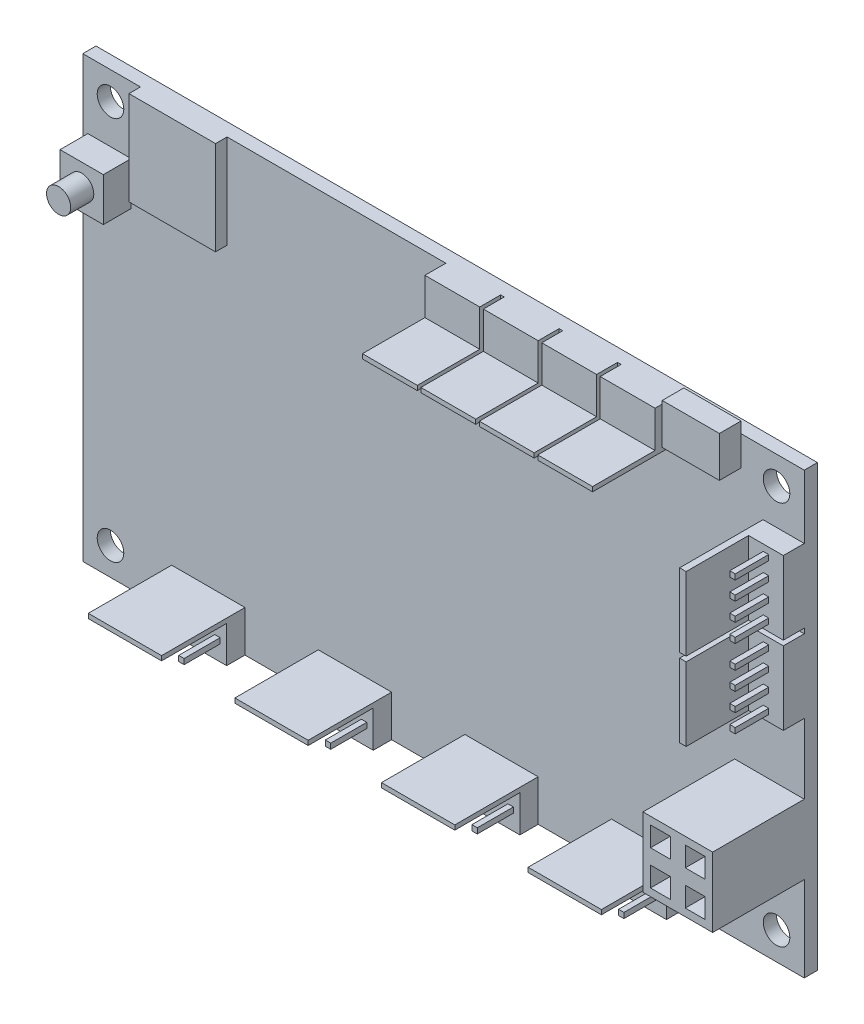
SolidWorks part; units mm, degrees
ref_plane "Front Plane" through (0, 0, 0) normal (0, 0, 1) x (1, 0, 0)
ref_plane "Top Plane" through (0, 0, 0) normal (0, 1, 0) x (1, 0, 0)
ref_plane "Right Plane" through (0, 0, 0) normal (1, 0, 0) x (0, 0, -1)
sketch "Sketch1" plane through (0, 0, 0) normal (0, 0, 1) x (1, 0, 0)
  line L1 (0, 0) -> (100, 0)
  line L2 (0, 0) -> (0, 60.96)
  line L3 (0, 60.96) -> (100, 60.96)
  line L4 (100, 0) -> (100, 60.96)
  dimension "D1" = 60.96
  dimension "D2" = 100
extrude "Boss-Extrude1" add sketch "Sketch1" along normal blind 1.8288
sketch "Sketch2" plane through (0, 0, 1.8288) normal (0, 0, 1) x (1, 0, 0)
  line L0 (0, 0) -> (100, 0) construction
  line L1 (12.319, 5.715) -> (22.479, 5.715)
  line L2 (12.319, 5.715) -> (12.319, 0)
  line L3 (12.319, 0) -> (22.479, 0)
  line L4 (22.479, 5.715) -> (22.479, 0)
  line L5 (12.319, 5.715) -> (22.479, 0) construction
  line L6 (12.319, 0) -> (22.479, 5.715) construction
  line L7 (0, 60.96) -> (0, 0) construction
  line L8 (32.639, 5.715) -> (42.799, 0) construction
  line L9 (32.639, 0) -> (42.799, 5.715) construction
  line L10 (32.639, 5.715) -> (42.799, 5.715)
  line L11 (42.799, 5.715) -> (42.799, 0)
  line L12 (32.639, 0) -> (42.799, 0)
  line L13 (32.639, 5.715) -> (32.639, 0)
  line L14 (52.959, 5.715) -> (63.119, 0) construction
  line L15 (52.959, 0) -> (63.119, 5.715) construction
  line L16 (52.959, 5.715) -> (63.119, 5.715)
  line L17 (63.119, 5.715) -> (63.119, 0)
  line L18 (52.959, 0) -> (63.119, 0)
  line L19 (52.959, 5.715) -> (52.959, 0)
  line L20 (73.279, 5.715) -> (83.439, 0) construction
  line L21 (73.279, 0) -> (83.439, 5.715) construction
  line L22 (73.279, 5.715) -> (83.439, 5.715)
  line L23 (83.439, 5.715) -> (83.439, 0)
  line L24 (73.279, 0) -> (83.439, 0)
  line L25 (73.279, 5.715) -> (73.279, 0)
  line L26 (12.319, 5.715) -> (32.639, 5.715) construction
  line L27 (100, 0) -> (100, 60.96) construction
  line L28 (100, 52.16) -> (94.285, 52.16)
  line L29 (100, 52.16) -> (100, 42)
  line L30 (100, 42) -> (94.285, 42)
  line L31 (94.285, 52.16) -> (94.285, 42)
  line L32 (100, 52.16) -> (94.285, 42) construction
  line L33 (100, 42) -> (94.285, 52.16) construction
  line L34 (100, 60.96) -> (0, 60.96) construction
  line L35 (100, 41.32) -> (94.285, 41.32)
  line L36 (100, 41.32) -> (100, 31.16)
  line L37 (100, 31.16) -> (94.285, 31.16)
  line L38 (94.285, 41.32) -> (94.285, 31.16)
  line L39 (100, 41.32) -> (94.285, 31.16) construction
  line L40 (100, 31.16) -> (94.285, 41.32) construction
  point P4 (17.399, 2.8575)
  point P27 (97.1425, 47.08)
  point P34 (97.1425, 36.24)
  dimension "D1" = 10.16
  dimension "D2" = 5.715
  dimension "D3" = 12.319
  dimension "D5" = 20.32
  dimension "D6" = 21
  dimension "D7" = 8.8
  dimension "D4" = 4
extrude "4 pin molex" add sketch "Sketch2" along normal blind 11.557
sketch "Sketch3" plane through (83.439, 0, 0) normal (1, 0, 0) x (0, 0, -1)
  line L0 (-13.3858, 5.715) -> (-1.8288, 5.715) construction
  line L1 (-13.3858, 0) -> (-4.3688, 0)
  line L2 (-13.3858, 0) -> (-13.3858, 5.08)
  line L3 (-13.3858, 5.08) -> (-4.3688, 5.08)
  line L4 (-4.3688, 0) -> (-4.3688, 5.08)
  line L5 (-13.3858, 0) -> (-4.3688, 5.08) construction
  line L6 (-13.3858, 5.08) -> (-4.3688, 0) construction
  line L7 (-1.8288, 0) -> (-1.8288, 31.16) construction
  point P4 (-8.8773, 2.54)
  dimension "D1" = 0.635
  dimension "D2" = 2.54
extrude "Cut-Extrude1" cut sketch "Sketch3" against normal through all
sketch "Sketch7" plane through (0, 31.16, 0) normal (0, -1, 0) x (-1, 0, 0)
  line L1 (-100, -13.3858) -> (-95.185, -13.3858)
  line L2 (-100, -13.3858) -> (-100, -4.7288)
  line L3 (-100, -4.7288) -> (-95.185, -4.7288)
  line L4 (-95.185, -13.3858) -> (-95.185, -4.7288)
  line L5 (-100, -13.3858) -> (-95.185, -4.7288) construction
  line L6 (-100, -4.7288) -> (-95.185, -13.3858) construction
  line L8 (-94.285, -13.3858) -> (-94.285, -1.8288) construction
  line L9 (-83.439, -1.8288) -> (-100, -1.8288) construction
  point P4 (-97.5925, -9.0573)
  dimension "D1" = 0.9
  dimension "D2" = 2.9
extrude "Cut-Extrude2" cut sketch "Sketch7" against normal blind 24.6
sketch "Sketch4" plane through (0, 0, 1.8288) normal (0, 0, 1) x (1, 0, 0)
  line L0 (100, 0) -> (100, 31.16) construction
  line L1 (100, 21.463) -> (90.348, 21.463)
  line L2 (100, 21.463) -> (100, 11.811)
  line L3 (100, 11.811) -> (90.348, 11.811)
  line L4 (90.348, 21.463) -> (90.348, 11.811)
  line L5 (100, 21.463) -> (90.348, 11.811) construction
  line L6 (100, 11.811) -> (90.348, 21.463) construction
  line L7 (83.439, 0) -> (100, 0) construction
  point P4 (95.174, 16.637)
  dimension "D1" = 9.652
  dimension "D2" = 9.652
  dimension "D3" = 11.811
extrude "Power Connector" add sketch "Sketch4" along normal blind 12.7
sketch "Sketch5" plane through (0, 0, 1.8288) normal (0, 0, 1) x (1, 0, 0)
  line L0 (100, 21.463) -> (100, 31.16) construction
  line L1 (83.3122, 56.8452) -> (91.237, 56.8452)
  line L2 (83.3122, 56.8452) -> (83.3122, 62.484)
  line L3 (83.3122, 62.484) -> (91.237, 62.484)
  line L4 (91.237, 56.8452) -> (91.237, 62.484)
  line L5 (83.3122, 56.8452) -> (91.237, 62.484) construction
  line L6 (83.3122, 62.484) -> (91.237, 56.8452) construction
  line L7 (100, 60.96) -> (0, 60.96) construction
  point P4 (87.2746, 59.6646)
  dimension "D1" = 7.9248
  dimension "D2" = 5.6388
  dimension "D3" = 8.763
  dimension "D4" = 1.524
extrude "MicroUSB" add sketch "Sketch5" along normal blind 3
sketch "Sketch6" plane through (0, 0, 1.8288) normal (0, 0, 1) x (1, 0, 0)
  line L0 (83.3122, 60.96) -> (0, 60.96) construction
  line L1 (8, 60.96) -> (20, 60.96)
  line L2 (8, 60.96) -> (8, 47.96)
  line L3 (8, 47.96) -> (20, 47.96)
  line L4 (20, 60.96) -> (20, 47.96)
  line L5 (8, 60.96) -> (20, 47.96) construction
  line L6 (8, 47.96) -> (20, 60.96) construction
  line L7 (0, 60.96) -> (0, 0) construction
  point P4 (14, 54.46)
  dimension "D1" = 12
  dimension "D2" = 13
  dimension "D3" = 8
extrude "MicroSD" add sketch "Sketch6" along normal blind 1.6
sketch "Sketch8" plane through (0, 0, 1.8288) normal (0, 0, 1) x (1, 0, 0)
  line L0 (0, 60.96) -> (0, 0) construction
  line L1 (0.7, 51.71) -> (6.7, 51.71)
  line L2 (0.7, 51.71) -> (0.7, 45.71)
  line L3 (0.7, 45.71) -> (6.7, 45.71)
  line L4 (6.7, 51.71) -> (6.7, 45.71)
  line L5 (0.7, 51.71) -> (6.7, 45.71) construction
  line L6 (0.7, 45.71) -> (6.7, 51.71) construction
  line L7 (8, 60.96) -> (0, 60.96) construction
  point P4 (3.7, 48.71)
  dimension "D1" = 6
  dimension "D2" = 6
  dimension "D3" = 6.7
  dimension "D4" = 9.25
extrude "Boss-Extrude6" add sketch "Sketch8" along normal blind 3.85
sketch "Sketch9" plane through (0, 0, 5.6788) normal (0, 0, 1) x (1, 0, 0)
  line L0 (0.7, 48.71) -> (3.7, 48.71) construction
  line L1 (0.7, 51.71) -> (0.7, 45.71) construction
  line L2 (3.7, 48.71) -> (3.7, 51.71) construction
  line L3 (6.7, 51.71) -> (0.7, 51.71) construction
  circle A0 centre (3.7, 48.71) radius 1.675
  dimension "D1" = 3.35
extrude "Boss-Extrude7" add sketch "Sketch9" along normal blind 3.2
sketch "Sketch10" plane through (0, 0, 1.8288) normal (0, 0, 1) x (1, 0, 0)
  line L0 (83.3122, 60.96) -> (20, 60.96) construction
  line L1 (82.22, 60.96) -> (74.62, 60.96)
  line L2 (82.22, 60.96) -> (82.22, 55.245)
  line L3 (82.22, 55.245) -> (74.62, 55.245)
  line L4 (74.62, 60.96) -> (74.62, 55.245)
  line L5 (82.22, 60.96) -> (74.62, 55.245) construction
  line L6 (82.22, 55.245) -> (74.62, 60.96) construction
  line L7 (100, 52.16) -> (100, 60.96) construction
  line L8 (74.12, 55.245) -> (66.52, 55.245)
  line L9 (66.52, 60.96) -> (66.52, 55.245)
  line L10 (74.12, 55.245) -> (66.52, 60.96) construction
  line L11 (74.12, 60.96) -> (66.52, 55.245) construction
  line L12 (74.12, 60.96) -> (66.52, 60.96)
  line L13 (74.12, 60.96) -> (74.12, 55.245)
  line L14 (66.02, 55.245) -> (58.42, 55.245)
  line L15 (58.42, 60.96) -> (58.42, 55.245)
  line L16 (66.02, 55.245) -> (58.42, 60.96) construction
  line L17 (66.02, 60.96) -> (58.42, 55.245) construction
  line L18 (66.02, 60.96) -> (58.42, 60.96)
  line L19 (66.02, 60.96) -> (66.02, 55.245)
  line L20 (57.92, 55.245) -> (50.32, 55.245)
  line L21 (50.32, 60.96) -> (50.32, 55.245)
  line L22 (57.92, 55.245) -> (50.32, 60.96) construction
  line L23 (57.92, 60.96) -> (50.32, 55.245) construction
  line L24 (57.92, 60.96) -> (50.32, 60.96)
  line L25 (57.92, 60.96) -> (57.92, 55.245)
  line L26 (82.22, 55.245) -> (74.12, 55.245) construction
  point P4 (78.42, 58.1025)
  dimension "D1" = 7.6
  dimension "D2" = 5.715
  dimension "D3" = 17.78
  dimension "D5" = 8.1
  dimension "D4" = 4
extrude "Boss-Extrude8" add sketch "Sketch10" along normal blind 11.557
sketch "Sketch11" plane through (82.22, 0, 0) normal (1, 0, 0) x (0, 0, -1)
  line L0 (-13.3858, 55.245) -> (-1.8288, 55.245) construction
  line L1 (-13.3858, 60.96) -> (-4.7288, 60.96)
  line L2 (-13.3858, 60.96) -> (-13.3858, 55.88)
  line L3 (-13.3858, 55.88) -> (-4.7288, 55.88)
  line L4 (-4.7288, 60.96) -> (-4.7288, 55.88)
  line L5 (-13.3858, 60.96) -> (-4.7288, 55.88) construction
  line L6 (-13.3858, 55.88) -> (-4.7288, 60.96) construction
  line L7 (-1.8288, 52.16) -> (-1.8288, 60.96) construction
  point P4 (-9.0573, 58.42)
  dimension "D1" = 0.635
  dimension "D2" = 2.9
extrude "Cut-Extrude3" cut sketch "Sketch11" against normal blind 36.449
sketch "Sketch13" plane through (0, 0, 1.8288) normal (0, 0, 1) x (1, 0, 0)
  line L0 (8, 60.96) -> (0, 60.96) construction
  line L1 (0, 60.96) -> (0, 0) construction
  line L2 (100, 0) -> (100, 11.811) construction
  line L3 (83.439, 0) -> (100, 0) construction
  circle A0 centre (3.8415, 57.1185) radius 1.8415
  circle A1 centre (3.8415, 3.8415) radius 1.8415
  circle A2 centre (96.1585, 3.8415) radius 1.8415
  circle A3 centre (96.1585, 57.1185) radius 1.8415
  dimension "D1" = 3.683
  dimension "D2" = 2
  dimension "D3" = 2
  dimension "D4" = 2
  dimension "D5" = 2
extrude "Cut-Extrude4" cut sketch "Sketch13" against normal blind 36.449
sketch "Sketch14" plane through (0, 0, 14.5288) normal (0, 0, 1) x (1, 0, 0)
  line L0 (96.212, 20.425) -> (98.962, 17.675) construction
  line L1 (90.348, 21.463) -> (100, 21.463)
  line L2 (90.348, 21.463) -> (90.348, 11.811)
  line L3 (90.348, 11.811) -> (100, 11.811)
  line L4 (100, 21.463) -> (100, 11.811)
  line L5 (95.174, 11.811) -> (95.174, 21.463) construction
  line L6 (90.348, 16.637) -> (100, 16.637) construction
  line L7 (92.761, 14.224) -> (97.587, 14.224) construction
  line L8 (92.761, 14.224) -> (92.761, 19.05) construction
  line L9 (92.761, 19.05) -> (97.587, 19.05) construction
  line L10 (97.587, 14.224) -> (97.587, 19.05) construction
  line L11 (92.761, 14.224) -> (97.587, 19.05) construction
  line L12 (92.761, 19.05) -> (97.587, 14.224) construction
  line L13 (91.386, 17.675) -> (94.136, 17.675)
  line L14 (91.386, 17.675) -> (91.386, 20.425)
  line L15 (91.386, 20.425) -> (94.136, 20.425)
  line L16 (94.136, 17.675) -> (94.136, 20.425)
  line L17 (91.386, 17.675) -> (94.136, 20.425) construction
  line L18 (91.386, 20.425) -> (94.136, 17.675) construction
  line L19 (96.212, 17.675) -> (98.962, 20.425) construction
  line L20 (96.212, 17.675) -> (98.962, 17.675)
  line L21 (96.212, 17.675) -> (96.212, 20.425)
  line L22 (96.212, 20.425) -> (98.962, 20.425)
  line L23 (98.962, 17.675) -> (98.962, 20.425)
  line L24 (96.212, 15.599) -> (98.962, 12.849) construction
  line L25 (96.212, 12.849) -> (98.962, 15.599) construction
  line L26 (96.212, 12.849) -> (98.962, 12.849)
  line L27 (96.212, 12.849) -> (96.212, 15.599)
  line L28 (96.212, 15.599) -> (98.962, 15.599)
  line L29 (98.962, 12.849) -> (98.962, 15.599)
  line L30 (91.386, 15.599) -> (94.136, 12.849) construction
  line L31 (91.386, 12.849) -> (94.136, 15.599) construction
  line L32 (91.386, 12.849) -> (94.136, 12.849)
  line L33 (91.386, 12.849) -> (91.386, 15.599)
  line L34 (91.386, 15.599) -> (94.136, 15.599)
  line L35 (94.136, 12.849) -> (94.136, 15.599)
  line L36 (91.386, 20.425) -> (96.212, 20.425) construction
  line L37 (91.386, 20.425) -> (91.386, 15.599) construction
  point P4 (95.174, 16.637)
  point P56 (95.174, 16.637)
  dimension "D1" = 4.826
  dimension "D2" = 2.75
  dimension "D5" = 90
  dimension "D6" = 4.826
  dimension "D7" = 4.826
  dimension "D3" = 2
  dimension "D4" = 2
extrude "Cut-Extrude5" cut sketch "Sketch14" against normal blind 5 contours L26 L29 L28 L27 | L32 L35 L34 L33 | L13 L16 L15 L14 | L20 L23 L22 L21
sketch "Sketch15" plane through (0, 0, 4.3688) normal (0, 0, 1) x (1, 0, 0)
  line L0 (52.959, 0) -> (52.959, 5.08) construction
  line L1 (22.479, 0) -> (12.319, 0)
  line L2 (22.479, 0) -> (22.479, 5.08)
  line L3 (22.479, 5.08) -> (12.319, 5.08)
  line L4 (12.319, 0) -> (12.319, 5.08)
  line L5 (17.399, 5.08) -> (17.399, 0) construction
  line L6 (22.479, 2.54) -> (12.319, 2.54) construction
  line L7 (42.799, 0) -> (32.639, 0)
  line L8 (42.799, 0) -> (42.799, 5.08)
  line L9 (42.799, 5.08) -> (32.639, 5.08)
  line L10 (32.639, 0) -> (32.639, 5.08)
  line L11 (37.719, 5.08) -> (37.719, 0) construction
  line L12 (42.799, 2.54) -> (32.639, 2.54) construction
  line L13 (63.119, 0) -> (52.959, 0)
  line L14 (63.119, 0) -> (63.119, 5.08)
  line L15 (63.119, 5.08) -> (52.959, 5.08)
  line L16 (52.959, 0) -> (52.959, 5.08)
  line L17 (58.039, 5.08) -> (58.039, 0) construction
  line L18 (63.119, 2.54) -> (52.959, 2.54) construction
  line L19 (52.959, 5.715) -> (52.959, 0) construction
  line L20 (94.285, 31.16) -> (100, 31.16) construction
  line L21 (83.439, 0) -> (73.279, 0)
  line L22 (83.439, 0) -> (83.439, 5.08)
  line L23 (83.439, 5.08) -> (73.279, 5.08)
  line L24 (73.279, 0) -> (73.279, 5.08)
  line L25 (78.359, 5.08) -> (78.359, 0) construction
  line L26 (83.439, 2.54) -> (73.279, 2.54) construction
  line L27 (100, 41.32) -> (95.185, 41.32)
  line L28 (100, 41.32) -> (100, 31.16)
  line L29 (100, 31.16) -> (95.185, 31.16)
  line L30 (95.185, 41.32) -> (95.185, 31.16)
  line L31 (97.5925, 31.16) -> (97.5925, 41.32) construction
  line L32 (100, 36.24) -> (95.185, 36.24) construction
  line L33 (94.285, 31.16) -> (95.185, 31.16) construction
  line L34 (100, 41.32) -> (94.285, 41.32) construction
  line L35 (95.185, 42) -> (100, 42)
  line L36 (95.185, 42) -> (95.185, 52.16)
  line L37 (95.185, 52.16) -> (100, 52.16)
  line L38 (100, 42) -> (100, 52.16)
  line L39 (97.5925, 52.16) -> (97.5925, 42) construction
  line L40 (95.185, 47.08) -> (100, 47.08) construction
  point P9 (54.229, 2.54)
  point P56 (56.769, 2.54)
  point P61 (59.309, 2.54)
  point P66 (61.849, 2.54)
  point P88 (37.719, 2.54)
  point P93 (58.039, 2.54)
  point P104 (54.229, 2.54)
  point P105 (78.359, 2.54)
  point P183 (97.5925, 47.08)
  point P207 (97.5925, 36.24)
  line B0 (57.144, 2.165) -> (56.394, 2.165)
  line B1 (54.604, 2.165) -> (53.854, 2.165)
  line B2 (54.604, 2.165) -> (54.604, 2.915)
  line B3 (54.604, 2.915) -> (53.854, 2.915)
  line B4 (53.854, 2.165) -> (53.854, 2.915)
  line B5 (57.144, 2.165) -> (57.144, 2.915)
  line B6 (57.144, 2.915) -> (56.394, 2.915)
  line B7 (56.394, 2.165) -> (56.394, 2.915)
  line B8 (59.684, 2.165) -> (58.934, 2.165)
  line B9 (59.684, 2.165) -> (59.684, 2.915)
  line B10 (59.684, 2.915) -> (58.934, 2.915)
  line B11 (58.934, 2.165) -> (58.934, 2.915)
  line B12 (62.224, 2.165) -> (61.474, 2.165)
  line B13 (62.224, 2.165) -> (62.224, 2.915)
  line B14 (62.224, 2.915) -> (61.474, 2.915)
  line B15 (61.474, 2.165) -> (61.474, 2.915)
  line B16 (54.604, 2.165) -> (53.854, 2.915) construction
  line B17 (54.604, 2.915) -> (53.854, 2.165) construction
  line B18 (57.144, 2.165) -> (56.394, 2.915) construction
  line B19 (57.144, 2.915) -> (56.394, 2.165) construction
  line B20 (59.684, 2.165) -> (58.934, 2.915) construction
  line B21 (59.684, 2.915) -> (58.934, 2.165) construction
  line B22 (62.224, 2.165) -> (61.474, 2.915) construction
  line B23 (62.224, 2.915) -> (61.474, 2.165) construction
  line B24 (54.229, 2.54) -> (56.769, 2.54) construction
  line B25 (97.9675, 35.345) -> (97.9675, 34.595)
  line B26 (97.9675, 32.805) -> (97.9675, 32.055)
  line B27 (97.9675, 32.805) -> (97.2175, 32.805)
  line B28 (97.2175, 32.805) -> (97.2175, 32.055)
  line B29 (97.9675, 32.055) -> (97.2175, 32.055)
  line B30 (97.9675, 35.345) -> (97.2175, 35.345)
  line B31 (97.2175, 35.345) -> (97.2175, 34.595)
  line B32 (97.9675, 34.595) -> (97.2175, 34.595)
  line B33 (97.9675, 37.885) -> (97.9675, 37.135)
  line B34 (97.9675, 37.885) -> (97.2175, 37.885)
  line B35 (97.2175, 37.885) -> (97.2175, 37.135)
  line B36 (97.9675, 37.135) -> (97.2175, 37.135)
  line B37 (97.9675, 40.425) -> (97.9675, 39.675)
  line B38 (97.9675, 40.425) -> (97.2175, 40.425)
  line B39 (97.2175, 40.425) -> (97.2175, 39.675)
  line B40 (97.9675, 39.675) -> (97.2175, 39.675)
  line B41 (97.9675, 32.805) -> (97.2175, 32.055) construction
  line B42 (97.2175, 32.805) -> (97.9675, 32.055) construction
  line B43 (97.9675, 35.345) -> (97.2175, 34.595) construction
  line B44 (97.2175, 35.345) -> (97.9675, 34.595) construction
  line B45 (97.9675, 37.885) -> (97.2175, 37.135) construction
  line B46 (97.2175, 37.885) -> (97.9675, 37.135) construction
  line B47 (97.9675, 40.425) -> (97.2175, 39.675) construction
  line B48 (97.2175, 40.425) -> (97.9675, 39.675) construction
  line B49 (97.5925, 32.43) -> (97.5925, 34.97) construction
  line B50 (97.9675, 46.185) -> (97.9675, 45.435)
  line B51 (97.9675, 43.645) -> (97.9675, 42.895)
  line B52 (97.9675, 43.645) -> (97.2175, 43.645)
  line B53 (97.2175, 43.645) -> (97.2175, 42.895)
  line B54 (97.9675, 42.895) -> (97.2175, 42.895)
  line B55 (97.9675, 46.185) -> (97.2175, 46.185)
  line B56 (97.2175, 46.185) -> (97.2175, 45.435)
  line B57 (97.9675, 45.435) -> (97.2175, 45.435)
  line B58 (97.9675, 48.725) -> (97.9675, 47.975)
  line B59 (97.9675, 48.725) -> (97.2175, 48.725)
  line B60 (97.2175, 48.725) -> (97.2175, 47.975)
  line B61 (97.9675, 47.975) -> (97.2175, 47.975)
  line B62 (97.9675, 51.265) -> (97.9675, 50.515)
  line B63 (97.9675, 51.265) -> (97.2175, 51.265)
  line B64 (97.2175, 51.265) -> (97.2175, 50.515)
  line B65 (97.9675, 50.515) -> (97.2175, 50.515)
  line B66 (97.9675, 43.645) -> (97.2175, 42.895) construction
  line B67 (97.2175, 43.645) -> (97.9675, 42.895) construction
  line B68 (97.9675, 46.185) -> (97.2175, 45.435) construction
  line B69 (97.2175, 46.185) -> (97.9675, 45.435) construction
  line B70 (97.9675, 48.725) -> (97.2175, 47.975) construction
  line B71 (97.2175, 48.725) -> (97.9675, 47.975) construction
  line B72 (97.9675, 51.265) -> (97.2175, 50.515) construction
  line B73 (97.2175, 51.265) -> (97.9675, 50.515) construction
  line B74 (97.5925, 43.27) -> (97.5925, 45.81) construction
  line B75 (16.504, 2.165) -> (15.754, 2.165)
  line B76 (13.964, 2.165) -> (13.214, 2.165)
  line B77 (13.964, 2.165) -> (13.964, 2.915)
  line B78 (13.964, 2.915) -> (13.214, 2.915)
  line B79 (13.214, 2.165) -> (13.214, 2.915)
  line B80 (16.504, 2.165) -> (16.504, 2.915)
  line B81 (16.504, 2.915) -> (15.754, 2.915)
  line B82 (15.754, 2.165) -> (15.754, 2.915)
  line B83 (19.044, 2.165) -> (18.294, 2.165)
  line B84 (19.044, 2.165) -> (19.044, 2.915)
  line B85 (19.044, 2.915) -> (18.294, 2.915)
  line B86 (18.294, 2.165) -> (18.294, 2.915)
  line B87 (21.584, 2.165) -> (20.834, 2.165)
  line B88 (21.584, 2.165) -> (21.584, 2.915)
  line B89 (21.584, 2.915) -> (20.834, 2.915)
  line B90 (20.834, 2.165) -> (20.834, 2.915)
  line B91 (13.964, 2.165) -> (13.214, 2.915) construction
  line B92 (13.964, 2.915) -> (13.214, 2.165) construction
  line B93 (16.504, 2.165) -> (15.754, 2.915) construction
  line B94 (16.504, 2.915) -> (15.754, 2.165) construction
  line B95 (19.044, 2.165) -> (18.294, 2.915) construction
  line B96 (19.044, 2.915) -> (18.294, 2.165) construction
  line B97 (21.584, 2.165) -> (20.834, 2.915) construction
  line B98 (21.584, 2.915) -> (20.834, 2.165) construction
  line B99 (13.589, 2.54) -> (16.129, 2.54) construction
  line B100 (36.824, 2.165) -> (36.074, 2.165)
  line B101 (34.284, 2.165) -> (33.534, 2.165)
  line B102 (34.284, 2.165) -> (34.284, 2.915)
  line B103 (34.284, 2.915) -> (33.534, 2.915)
  line B104 (33.534, 2.165) -> (33.534, 2.915)
  line B105 (36.824, 2.165) -> (36.824, 2.915)
  line B106 (36.824, 2.915) -> (36.074, 2.915)
  line B107 (36.074, 2.165) -> (36.074, 2.915)
  line B108 (39.364, 2.165) -> (38.614, 2.165)
  line B109 (39.364, 2.165) -> (39.364, 2.915)
  line B110 (39.364, 2.915) -> (38.614, 2.915)
  line B111 (38.614, 2.165) -> (38.614, 2.915)
  line B112 (41.904, 2.165) -> (41.154, 2.165)
  line B113 (41.904, 2.165) -> (41.904, 2.915)
  line B114 (41.904, 2.915) -> (41.154, 2.915)
  line B115 (41.154, 2.165) -> (41.154, 2.915)
  line B116 (34.284, 2.165) -> (33.534, 2.915) construction
  line B117 (34.284, 2.915) -> (33.534, 2.165) construction
  line B118 (36.824, 2.165) -> (36.074, 2.915) construction
  line B119 (36.824, 2.915) -> (36.074, 2.165) construction
  line B120 (39.364, 2.165) -> (38.614, 2.915) construction
  line B121 (39.364, 2.915) -> (38.614, 2.165) construction
  line B122 (41.904, 2.165) -> (41.154, 2.915) construction
  line B123 (41.904, 2.915) -> (41.154, 2.165) construction
  line B124 (33.909, 2.54) -> (36.449, 2.54) construction
  line B125 (77.464, 2.165) -> (76.714, 2.165)
  line B126 (74.924, 2.165) -> (74.174, 2.165)
  line B127 (74.924, 2.165) -> (74.924, 2.915)
  line B128 (74.924, 2.915) -> (74.174, 2.915)
  line B129 (74.174, 2.165) -> (74.174, 2.915)
  line B130 (77.464, 2.165) -> (77.464, 2.915)
  line B131 (77.464, 2.915) -> (76.714, 2.915)
  line B132 (76.714, 2.165) -> (76.714, 2.915)
  line B133 (80.004, 2.165) -> (79.254, 2.165)
  line B134 (80.004, 2.165) -> (80.004, 2.915)
  line B135 (80.004, 2.915) -> (79.254, 2.915)
  line B136 (79.254, 2.165) -> (79.254, 2.915)
  line B137 (82.544, 2.165) -> (81.794, 2.165)
  line B138 (82.544, 2.165) -> (82.544, 2.915)
  line B139 (82.544, 2.915) -> (81.794, 2.915)
  line B140 (81.794, 2.165) -> (81.794, 2.915)
  line B141 (74.924, 2.165) -> (74.174, 2.915) construction
  line B142 (74.924, 2.915) -> (74.174, 2.165) construction
  line B143 (77.464, 2.165) -> (76.714, 2.915) construction
  line B144 (77.464, 2.915) -> (76.714, 2.165) construction
  line B145 (80.004, 2.165) -> (79.254, 2.915) construction
  line B146 (80.004, 2.915) -> (79.254, 2.165) construction
  line B147 (82.544, 2.165) -> (81.794, 2.915) construction
  line B148 (82.544, 2.915) -> (81.794, 2.165) construction
  line B149 (74.549, 2.54) -> (77.089, 2.54) construction
sketch_block_instance "Block1-1"
sketch_block "Block1"
sketch_block_instance "4 pin molex-1"
sketch_block "Block2"
sketch_block_instance "Block2-1"
sketch_block_instance "Block2-4"
sketch_block_instance "Block2-5"
sketch_block_instance "Block2-6"
extrude "Boss-Extrude9" add sketch "Sketch15" along normal blind 5 contours B79 B76 B77 B78 | B82 B75 B80 B81 | B86 B83 B84 B85 | B90 B87 B88 B89 | B104 B101 B102 B103 | B107 B100 B105 B106 | B111 B108 B109 B110 | B115 B112 B113 B114 | B4 B1 B2 B3 | B7 B0 B5 B6 | B11 B8 B9 B10 | B15 B12 B13 B14 | B132 B125 B130 B131 | B129 B126 B127 B128 | B136 B133 B134 B135 | B140 B137 B138 B139 | B29 B26 B27 B28 | B32 B25 B30 B31 | B36 B33 B34 B35 | B40 B37 B38 B39 | B54 B51 B52 B53 | B57 B50 B55 B56 | B61 B58 B59 B60 | B65 B62 B63 B64
sketch "Sketch16" plane through (0, 62.484, 0) normal (0, 1, 0) x (1, 0, 0)
  line L0 (91.237, -4.8288) -> (91.237, -1.8288) construction
  line L1 (91.237, -4.8288) -> (83.3122, -4.8288)
  line L2 (91.237, -4.8288) -> (91.237, -1.8288)
  line L3 (91.237, -1.8288) -> (83.3122, -1.8288)
  line L4 (83.3122, -4.8288) -> (83.3122, -1.8288)
  line L5 (91.237, -4.8288) -> (83.3122, -1.8288) construction
  line L6 (91.237, -1.8288) -> (83.3122, -4.8288) construction
  line L7 (91.237, -4.8288) -> (83.3122, -4.8288) construction
  point P4 (87.2746, -3.3288)
